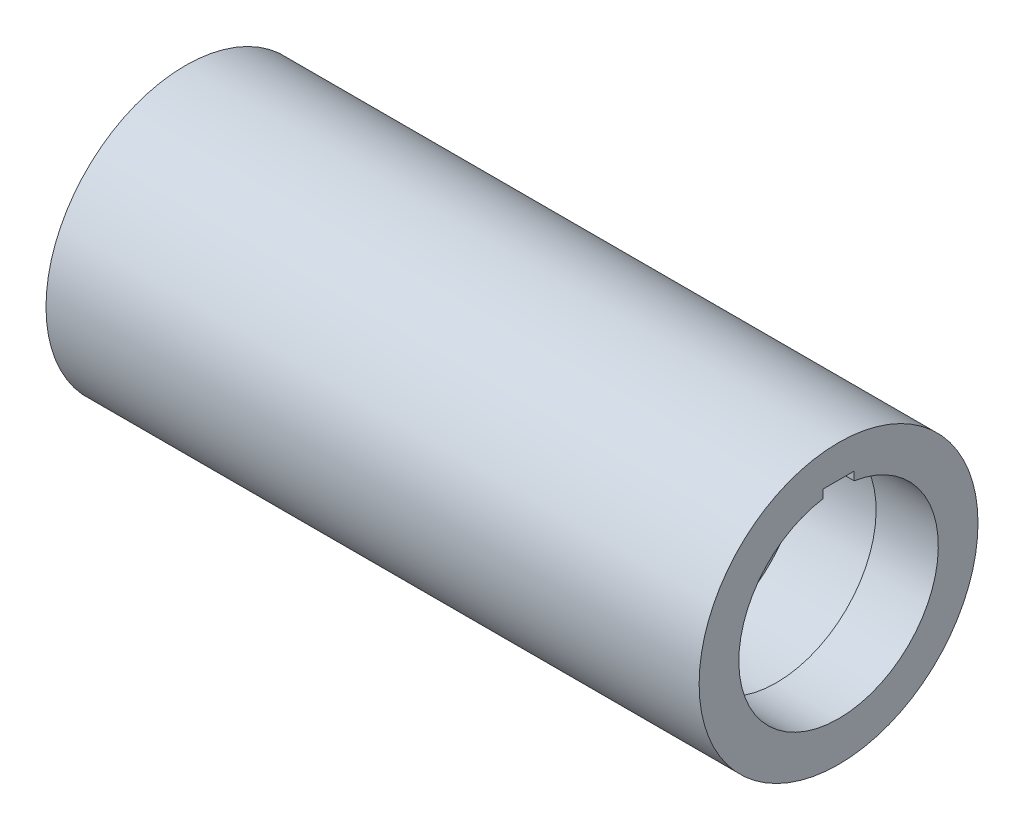
SolidWorks part; units mm, degrees
material "Phosphor bronze 10% D, UNS C52400"
ref_plane "Front" through (0, 0, 0) normal (0, 0, 1) x (1, 0, 0)
ref_plane "Top" through (0, 0, 0) normal (0, 1, 0) x (1, 0, 0)
ref_plane "Right" through (0, 0, 0) normal (1, 0, 0) x (0, 0, -1)
sketch "Sketch1" plane through (0, 0, 0) normal (0, 0, 1) x (1, 0, 0)
  line L0 (0, 33.6936) -> (0, -32.969) construction
  line L1 (-66.3727, 0) -> (68.1118, 0) construction
  line L2 (-31.5, 13.45) -> (31.5, 13.45)
  line L3 (31.5, 13.45) -> (31.5, 9.6216)
  line L4 (31.5, 9.6216) -> (25.5, 9.6216)
  line L5 (25.5, 9.6216) -> (25.5, 10.4216)
  line L6 (25.5, 10.4216) -> (17.5, 10.4216)
  line L7 (17.5, 10.4216) -> (17.5, 9.6216)
  line L8 (17.5, 9.6216) -> (-31.5, 9.6216)
  line L9 (-31.5, 9.6216) -> (-31.5, 13.45)
  point P15 (21.5, 10.4216)
  dimension "D1" = 63
  dimension "D2" = 8
  dimension "D3" = 0.8
  dimension "D4" = 26.9
  dimension "D5" = 19.2432
  dimension "D6" = 10
revolve "Revolve1" add sketch "Sketch1" angle 360 about L1
sketch "Sketch3" plane through (31.5, 0, 0) normal (1, 0, 0) x (0, 0, -1)
  line L0 (0, 15.1367) -> (0, -16.1706) construction
  line L2 (-1.5, 10.3119) -> (1.5, 10.3119)
  line L3 (-1.5, 10.3119) -> (-1.5, 8.7119)
  line L4 (-1.5, 8.7119) -> (1.5, 8.7119)
  line L5 (1.5, 10.3119) -> (1.5, 8.7119)
  line L6 (-1.5, 10.3119) -> (1.5, 8.7119) construction
  line L7 (-1.5, 8.7119) -> (1.5, 10.3119) construction
  point P3 (0, 9.5119)
  dimension "D1" = 3
  dimension "D2" = 0.8
extrude "Cut-Extrude1" cut sketch "Sketch3" against normal through all
